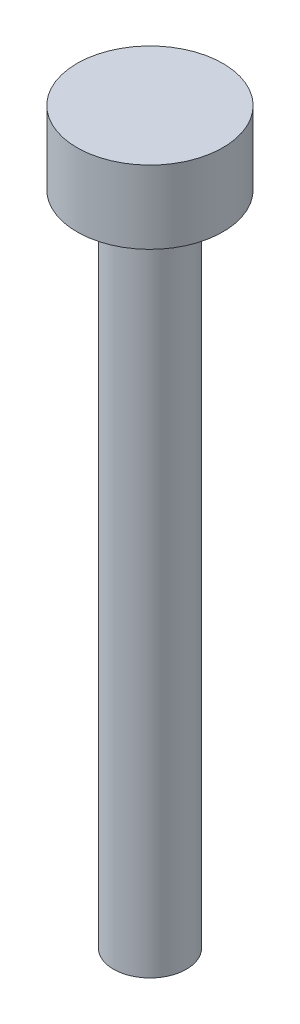
SolidWorks part; units mm, degrees
material "6061 Alloy"
ref_plane "Front Plane" through (0, 0, 0) normal (0, 0, 1) x (1, 0, 0)
ref_plane "Top Plane" through (0, 0, 0) normal (0, 1, 0) x (1, 0, 0)
ref_plane "Right Plane" through (0, 0, 0) normal (1, 0, 0) x (0, 0, -1)
sketch "Sketch1" plane through (0, 0, 0) normal (0, 0, 1) x (1, 0, 0)
  line L0 (0, 0) -> (0, 22.86)
  line L1 (0, 22.86) -> (-1.27, 22.86)
  line L2 (-1.27, 22.86) -> (-1.27, 25.4)
  line L3 (-1.27, 25.4) -> (1.27, 25.4)
  line L4 (1.27, 25.4) -> (1.27, 0)
  line L5 (1.27, 0) -> (0, 0)
  dimension "D1" = 1.27
  dimension "D2" = 25.4
  dimension "D3" = 2.54
  dimension "D4" = 1.27
revolve "Revolve1" add sketch "Sketch1" angle 360 about L4
